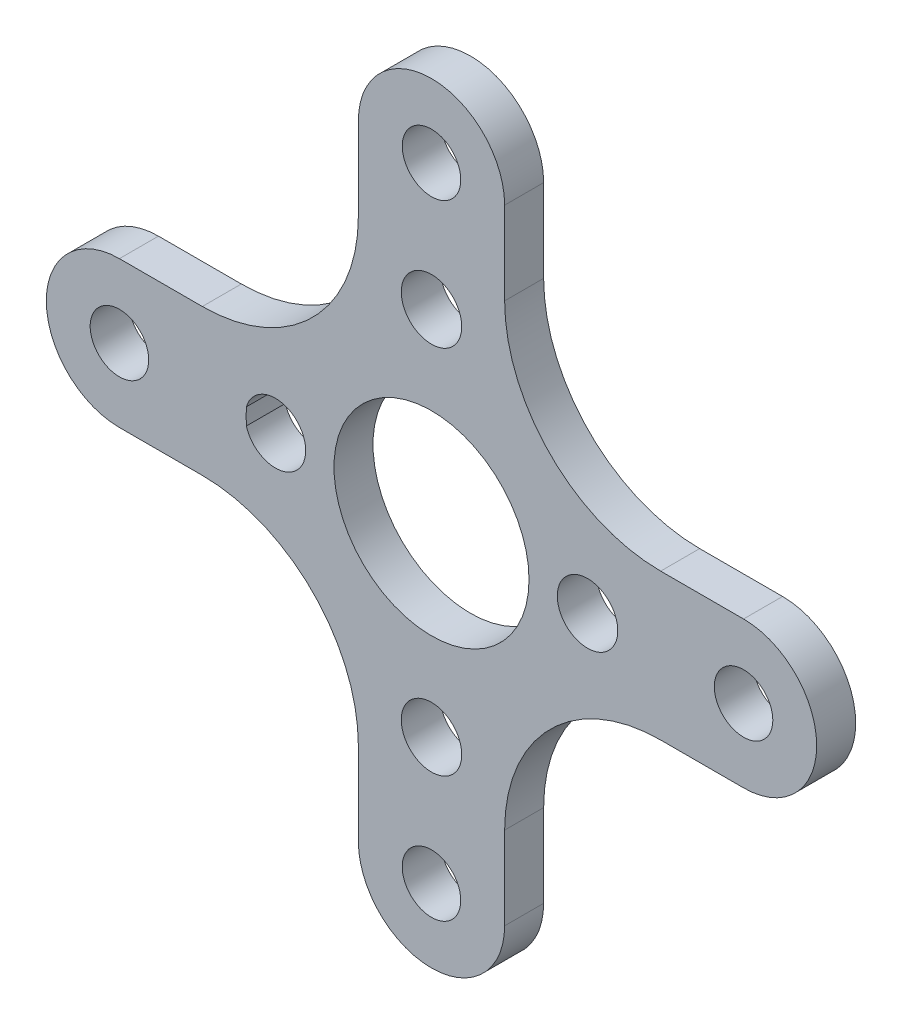
SolidWorks part; units mm, degrees
ref_plane "Front Plane" through (0, 0, 0) normal (0, 0, 1) x (1, 0, 0)
ref_plane "Top Plane" through (0, 0, 0) normal (0, 1, 0) x (1, 0, 0)
ref_plane "Right Plane" through (0, 0, 0) normal (1, 0, 0) x (0, 0, -1)
sketch "Sketch1" plane through (0, 0, 0) normal (0, 0, 1) x (1, 0, 0)
  line L0 (-3.75, 16) -> (-3.75, 11.75)
  line L1 (3.75, 16) -> (3.75, 11.75)
  line L2 (16, 3.75) -> (11.75, 3.75)
  line L3 (16, -3.75) -> (11.75, -3.75)
  line L4 (3.75, -16) -> (3.75, -11.75)
  line L5 (-3.75, -16) -> (-3.75, -11.75)
  line L6 (-16, -3.75) -> (-11.75, -3.75)
  line L7 (-16, 3.75) -> (-11.75, 3.75)
  circle A0 centre (0, 0) radius 5
  circle A1 centre (-16, 0) radius 1.5
  circle A2 centre (0, 16) radius 1.5
  circle A3 centre (16, 0) radius 1.5
  circle A4 centre (0, -16) radius 1.5
  arc A5 (3.75, 16) -> (-3.75, 16) centre (0, 16) ccw
  arc A6 (16, -3.75) -> (16, 3.75) centre (16, 0) ccw
  arc A7 (-3.75, -16) -> (3.75, -16) centre (0, -16) ccw
  arc A8 (-16, 3.75) -> (-16, -3.75) centre (-16, 0) ccw
  arc A9 (-3.75, 11.75) -> (-11.75, 3.75) centre (-11.75, 11.75) cw
  arc A10 (-3.75, -11.75) -> (-11.75, -3.75) centre (-11.75, -11.75) ccw
  arc A11 (11.75, -3.75) -> (3.75, -11.75) centre (11.75, -11.75) ccw
  arc A12 (3.75, 11.75) -> (11.75, 3.75) centre (11.75, 11.75) ccw
  point P14 (0, 0)
  point P34 (0, 0)
  dimension "D1" = 10
  dimension "D2" = 3
  dimension "D5" = 7.5
  dimension "D7" = 8
  dimension "D8" = 8
  dimension "D9" = 8
  dimension "D10" = 8
  dimension "D3" = 16
  dimension "D6" = 4
extrude "Boss-Extrude1" add sketch "Sketch1" along normal blind 2
sketch "Sketch3" plane through (0, 0, 0) normal (0, 0, -1) x (-1, 0, 0)
  circle A0 centre (0, 0) radius 8
  circle A1 centre (0, 0) radius 9.5
  circle A2 centre (0, 9.5) radius 1.55
  circle A3 centre (8, 0) radius 1.55
  circle A4 centre (0, -9.5) radius 1.55
  circle A5 centre (-8, 0) radius 1.55
  dimension "D1" = 16
  dimension "D2" = 19
  dimension "D3" = 3.1
  dimension "D4" = 3.1
  dimension "D5" = 3.1
  dimension "D6" = 3.1
extrude "Cut-Extrude1" cut sketch "Sketch3" against normal blind 10 contours A1 A4 | A1 A4 A0 | A0 A5 | A0 A5 A1 | A1 A5 | A0 A4 | A1 A3 A0 | A0 A3 | A2
